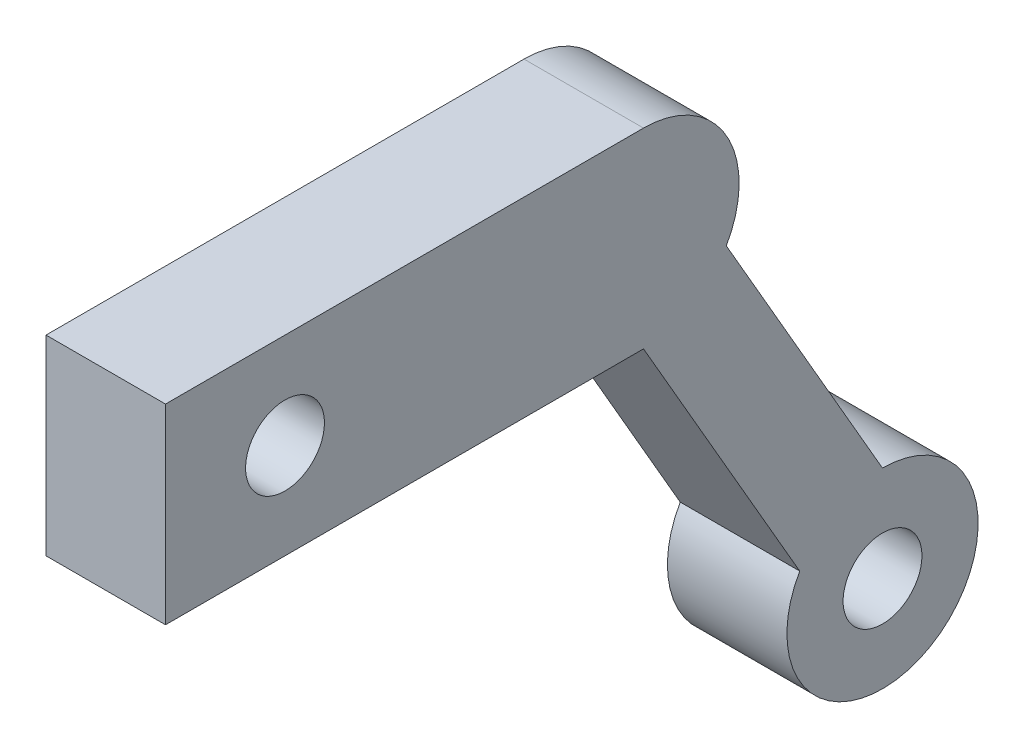
SolidWorks part; units mm, degrees
ref_plane "前视基准面" through (0, 0, 0) normal (0, 0, 1) x (1, 0, 0)
ref_plane "上视基准面" through (0, 0, 0) normal (0, 1, 0) x (1, 0, 0)
ref_plane "右视基准面" through (0, 0, 0) normal (1, 0, 0) x (0, 0, -1)
sketch "草图1" plane through (0, 0, 0) normal (1, 0, 0) x (0, 0, -1)
  line L0 (20, 0) -> (30, -17.3205)
  line L1 (0, 0) -> (20, 0)
  line L2 (0, 0) -> (0, -8)
  line L3 (0, -8) -> (20, -8)
  line L4 (20, 0) -> (20, -8)
  line L5 (20, 0) -> (20, -8)
  line L6 (30, -17.3205) -> (30, -25.3205)
  line L7 (20, -8) -> (30, -25.3205)
  circle A0 centre (30, -21.3205) radius 4
  circle A1 centre (20, -4) radius 4
  dimension "D1" = 8
  dimension "D2" = 20
  dimension "D3" = 150
  dimension "D4" = 20
extrude "凸台-拉伸1" add sketch "草图1" along normal blind 5 contours A1 L1 L2 L3 | L4 A1 | L4 A1 L0 | L0 A1 | A1 L7 A0 L0 | L6 A0 | L6 A0 L7 | L7 A0
sketch "草图2" plane through (5, 0, 0) normal (1, 0, 0) x (0, 0, -1)
  line L0 (0, 0) -> (0, -8) construction
  circle A0 centre (5, -4) radius 1.65
  circle A1 centre (30, -21.3205) radius 1.65
  dimension "D1" = 3.3
  dimension "D3" = 3.3
  dimension "D2" = 5
extrude "切除-拉伸1" cut sketch "草图2" against normal blind 10
